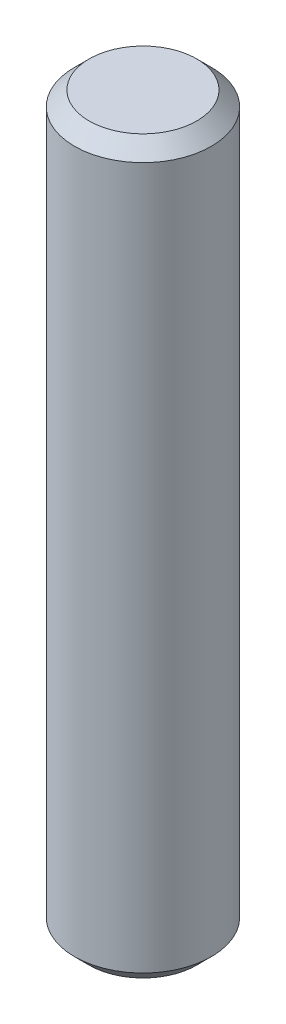
SolidWorks part; units mm, degrees
ref_plane "Front Plane" through (0, 0, 0) normal (0, 0, 1) x (1, 0, 0)
ref_plane "Top Plane" through (0, 0, 0) normal (0, 1, 0) x (1, 0, 0)
ref_plane "Right Plane" through (0, 0, 0) normal (1, 0, 0) x (0, 0, -1)
ref_plane "Plane1" through (0, 0, 0) normal (0, 0, -1) x (-1, 0, 0)
sketch "Sketch1" plane through (0, 0, 0) normal (0, 0, -1) x (-1, 0, 0)
  line L0 (-1.8694, 0) -> (0, 0)
  line L1 (0, 0) -> (0, 25.4)
  line L2 (0, 25.4) -> (-1.8694, 25.4)
  line L3 (-1.8694, 25.4) -> (-2.3774, 24.892)
  line L4 (-2.3774, 24.892) -> (-2.3774, 0.508)
  line L5 (-2.3774, 0.508) -> (-1.8694, 0)
  line L6 (0, 0) -> (0, 25.4) construction
revolve "Revolve1" add sketch "Sketch1" angle 360 about L6
